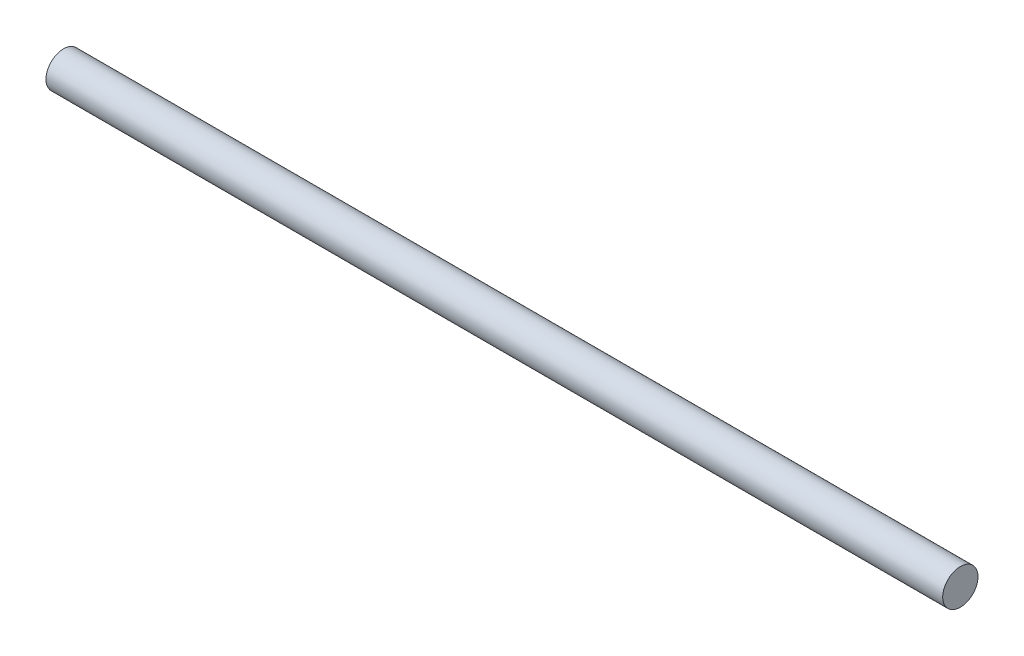
SolidWorks part; units mm, degrees
ref_plane "Front Plane" through (0, 0, 0) normal (0, 0, 1) x (1, 0, 0)
ref_plane "Top Plane" through (0, 0, 0) normal (0, 1, 0) x (1, 0, 0)
ref_plane "Right Plane" through (0, 0, 0) normal (1, 0, 0) x (0, 0, -1)
sketch "Sketch1" plane through (0, 0, 0) normal (1, 0, 0) x (0, 0, -1)
  circle A0 centre (0, 0) radius 2
  dimension "D1" = 4
extrude "Boss-Extrude1" add sketch "Sketch1" along normal blind 101.6
